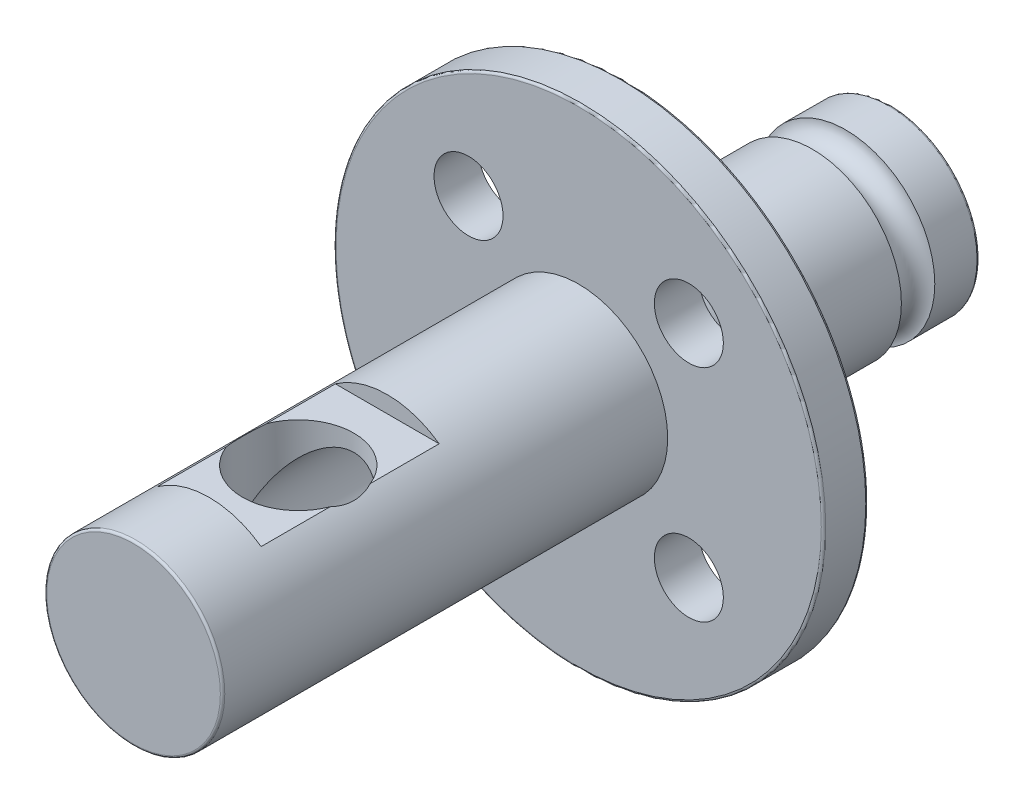
SolidWorks part; units mm, degrees
material "Stainless Steel (ferritic)"
ref_plane "Front Plane" through (0, 0, 0) normal (0, 0, 1) x (1, 0, 0)
ref_plane "Top Plane" through (0, 0, 0) normal (0, 1, 0) x (1, 0, 0)
ref_plane "Right Plane" through (0, 0, 0) normal (1, 0, 0) x (0, 0, -1)
sketch "Sketch2" plane through (0, 0, 0) normal (1, 0, 0) x (0, 0, -1)
  line L0 (-17, 0) -> (17, 0)
  line L1 (-17, 0) -> (-17, -4)
  line L2 (-17, -4) -> (3, -4)
  line L3 (3, -4) -> (3, -11)
  line L4 (3, -11) -> (5, -11)
  line L5 (5, -11) -> (5, -4)
  line L7 (17, 0) -> (17, -4)
  line L9 (5, -4) -> (13.5, -4)
  line L10 (15, -4) -> (17, -4)
  arc A1 (13.5, -4) -> (15, -4) centre (14.25, -4) cw
  point P4 (0, 0)
  dimension "D8" = 0.75
  dimension "D1" = 34
  dimension "D2" = 4
  dimension "D3" = 12
  dimension "D4" = 2
  dimension "D5" = 20
  dimension "D6" = 7
  dimension "D7" = 2.75
  dimension "D9" = 4
revolve "Revolve1" add sketch "Sketch2" angle 360 about L0
sketch "Sketch3" plane through (0, 0, -3) normal (0, 0, 1) x (1, 0, 0)
  circle A1 centre (-4.9497, 4.9497) radius 1.55
  circle A2 centre (4.9497, 4.9497) radius 1.55
  circle A3 centre (4.9497, -4.9497) radius 1.55
  circle A4 centre (-4.9497, -4.9497) radius 1.55
  point P16 (0, 0)
  dimension "D3" = 3.1
  dimension "D4" = 4
extrude "Cut-Extrude1" cut sketch "Sketch3" against normal blind 10
fillet "Fillet2" radius 0.1 4 edges at (4, 0, -17) (11, 0, -5) (11, 0, -3) (4, 0, 17)
ref_plane "Plane1" through (0, 4, 0) normal (0, 1, 0) x (1, 0, 0)
sketch "Sketch5" plane through (0, 4, 0) normal (0, 1, 0) x (1, 0, 0)
  line L0 (-4, 16.9) -> (4, 16.9) construction
  line L1 (-2.5, -13.6) -> (2.5, -13.6)
  line L2 (-2.5, -13.6) -> (-2.5, -5.6)
  line L3 (-2.5, -5.6) -> (2.5, -5.6)
  line L4 (2.5, -13.6) -> (2.5, -5.6)
  line L5 (-2.5, -13.6) -> (2.5, -5.6) construction
  line L6 (-2.5, -5.6) -> (2.5, -13.6) construction
  point P0 (0, -9.6)
  dimension "D1" = 8
  dimension "D2" = 5
  dimension "D3" = 26.5
extrude "Cut-Extrude3" cut sketch "Sketch5" against normal blind 0.75
sketch "Sketch6" plane through (0, 3.25, 0) normal (0, 1, 0) x (1, 0, 0)
  circle A0 centre (0, -9.6) radius 2.5
  dimension "D1" = 5
extrude "Cut-Extrude4" cut sketch "Sketch6" against normal blind 3.25
sketch "Sketch7" plane through (0, 0, -17) normal (0, 0, -1) x (-1, 0, 0)
  circle A0 centre (0, 0) radius 2.5
  dimension "D1" = 5
extrude "Cut-Extrude5" cut sketch "Sketch7" against normal blind 30
